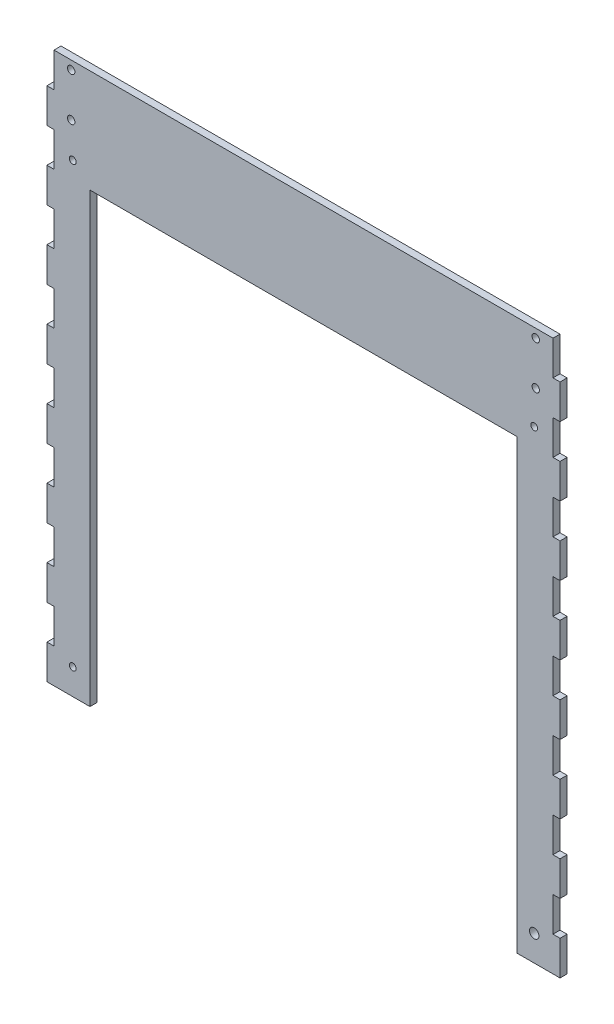
SolidWorks part; units mm, degrees
ref_plane "Front Plane" through (0, 0, 0) normal (0, 0, 1) x (1, 0, 0)
ref_plane "Top Plane" through (0, 0, 0) normal (0, 1, 0) x (1, 0, 0)
ref_plane "Right Plane" through (0, 0, 0) normal (1, 0, 0) x (0, 0, -1)
sketch "Sketch1" plane through (0, 0, 0) normal (0, 0, 1) x (1, 0, 0)
  line L0 (-184.15, 406.4) -> (-184.15, 0) construction
  line L1 (-189.357, 0) -> (189.357, 0)
  line L2 (-189.357, 0) -> (-189.357, 406.4)
  line L3 (-189.357, 406.4) -> (189.357, 406.4)
  line L4 (189.357, 0) -> (189.357, 406.4)
  line L5 (184.15, 0) -> (184.15, 406.4) construction
  line L7 (-157.607, 0) -> (157.607, 0)
  line L8 (-157.607, 0) -> (-157.607, 330.2)
  line L9 (-157.607, 330.2) -> (157.607, 330.2)
  line L10 (157.607, 0) -> (157.607, 330.2)
  line L14 (-184.15, 406.4) -> (-184.15, 381)
  line L15 (189.357, 406.4) -> (184.15, 406.4)
  line L16 (189.357, 406.4) -> (189.357, 381)
  line L17 (189.357, 381) -> (184.15, 381)
  line L18 (184.15, 406.4) -> (184.15, 381)
  line L19 (-184.15, 406.4) -> (-189.357, 406.4)
  line L20 (-189.357, 406.4) -> (-189.357, 381)
  line L21 (-184.15, 381) -> (-189.357, 381)
  line L22 (-184.15, 355.6) -> (-184.15, 330.2)
  line L23 (-184.15, 355.6) -> (-189.357, 355.6)
  line L24 (-189.357, 355.6) -> (-189.357, 330.2)
  line L25 (-184.15, 330.2) -> (-189.357, 330.2)
  line L26 (-184.15, 304.8) -> (-184.15, 279.4)
  line L27 (-184.15, 304.8) -> (-189.357, 304.8)
  line L28 (-189.357, 304.8) -> (-189.357, 279.4)
  line L29 (-184.15, 279.4) -> (-189.357, 279.4)
  line L30 (-184.15, 254) -> (-184.15, 228.6)
  line L31 (-184.15, 254) -> (-189.357, 254)
  line L32 (-189.357, 254) -> (-189.357, 228.6)
  line L33 (-184.15, 228.6) -> (-189.357, 228.6)
  line L34 (-184.15, 203.2) -> (-184.15, 177.8)
  line L35 (-184.15, 203.2) -> (-189.357, 203.2)
  line L36 (-189.357, 203.2) -> (-189.357, 177.8)
  line L37 (-184.15, 177.8) -> (-189.357, 177.8)
  line L38 (-184.15, 152.4) -> (-184.15, 127)
  line L39 (-184.15, 152.4) -> (-189.357, 152.4)
  line L40 (-189.357, 152.4) -> (-189.357, 127)
  line L41 (-184.15, 127) -> (-189.357, 127)
  line L42 (-184.15, 101.6) -> (-184.15, 76.2)
  line L43 (-184.15, 101.6) -> (-189.357, 101.6)
  line L44 (-189.357, 101.6) -> (-189.357, 76.2)
  line L45 (-184.15, 76.2) -> (-189.357, 76.2)
  line L46 (-184.15, 50.8) -> (-184.15, 25.4)
  line L47 (-184.15, 50.8) -> (-189.357, 50.8)
  line L48 (-189.357, 50.8) -> (-189.357, 25.4)
  line L49 (-184.15, 25.4) -> (-189.357, 25.4)
  line L50 (189.357, 355.6) -> (189.357, 330.2)
  line L51 (189.357, 355.6) -> (184.15, 355.6)
  line L52 (184.15, 355.6) -> (184.15, 330.2)
  line L53 (189.357, 330.2) -> (184.15, 330.2)
  line L54 (189.357, 304.8) -> (189.357, 279.4)
  line L55 (189.357, 304.8) -> (184.15, 304.8)
  line L56 (184.15, 304.8) -> (184.15, 279.4)
  line L57 (189.357, 279.4) -> (184.15, 279.4)
  line L58 (189.357, 254) -> (189.357, 228.6)
  line L59 (189.357, 254) -> (184.15, 254)
  line L60 (184.15, 254) -> (184.15, 228.6)
  line L61 (189.357, 228.6) -> (184.15, 228.6)
  line L62 (189.357, 203.2) -> (189.357, 177.8)
  line L63 (189.357, 203.2) -> (184.15, 203.2)
  line L64 (184.15, 203.2) -> (184.15, 177.8)
  line L65 (189.357, 177.8) -> (184.15, 177.8)
  line L66 (189.357, 152.4) -> (189.357, 127)
  line L67 (189.357, 152.4) -> (184.15, 152.4)
  line L68 (184.15, 152.4) -> (184.15, 127)
  line L69 (189.357, 127) -> (184.15, 127)
  line L70 (189.357, 101.6) -> (189.357, 76.2)
  line L71 (189.357, 101.6) -> (184.15, 101.6)
  line L72 (184.15, 101.6) -> (184.15, 76.2)
  line L73 (189.357, 76.2) -> (184.15, 76.2)
  line L74 (189.357, 50.8) -> (189.357, 25.4)
  line L75 (189.357, 50.8) -> (184.15, 50.8)
  line L76 (184.15, 50.8) -> (184.15, 25.4)
  line L77 (189.357, 25.4) -> (184.15, 25.4)
  circle A0 centre (-171.45, 400.05) radius 2.75
  circle A1 centre (-171.45, 368.05) radius 2.75
  circle A2 centre (171.45, 400.05) radius 2.75
  circle A3 centre (171.45, 368.05) radius 2.75
  circle A4 centre (170.307, 19.05) radius 3.5
  circle A5 centre (-170.307, 19.05) radius 2.5
  circle A6 centre (-170.307, 342.9) radius 2.5
  circle A7 centre (170.307, 342.9) radius 2.5
  point P5 (0, 0)
  point P16 (0, 330.2)
  point P17 (-189.357, 203.2)
  point P33 (0, 0)
  point P34 (-170.307, 342.0371)
  point P35 (-127.2848, 98.9906)
  point P36 (0, 0)
  point P37 (0, 0)
  point P38 (0, 0)
  point P39 (0, 0)
  dimension "D4" = 5.5
  dimension "D13" = 5
  dimension "D14" = 7
  dimension "D2" = 406.4
  dimension "D3" = 12.7
  dimension "D5" = 5.207
  dimension "D6" = 6.35
  dimension "D7" = 32
  dimension "D8" = 5.207
  dimension "D9" = 12.7
  dimension "D10" = 368.3
  dimension "D11" = 31.75
  dimension "D12" = 76.2
  dimension "D15" = 19.05
  dimension "D16" = 25.4
  dimension "D19" = 25.4
  dimension "D20" = 12.7
  dimension "D21" = 12.7
  dimension "D22" = 342.9
  dimension "D17" = 2
  dimension "D18" = 8
extrude "Boss-Extrude1" add sketch "Sketch1" along normal blind 5.207
